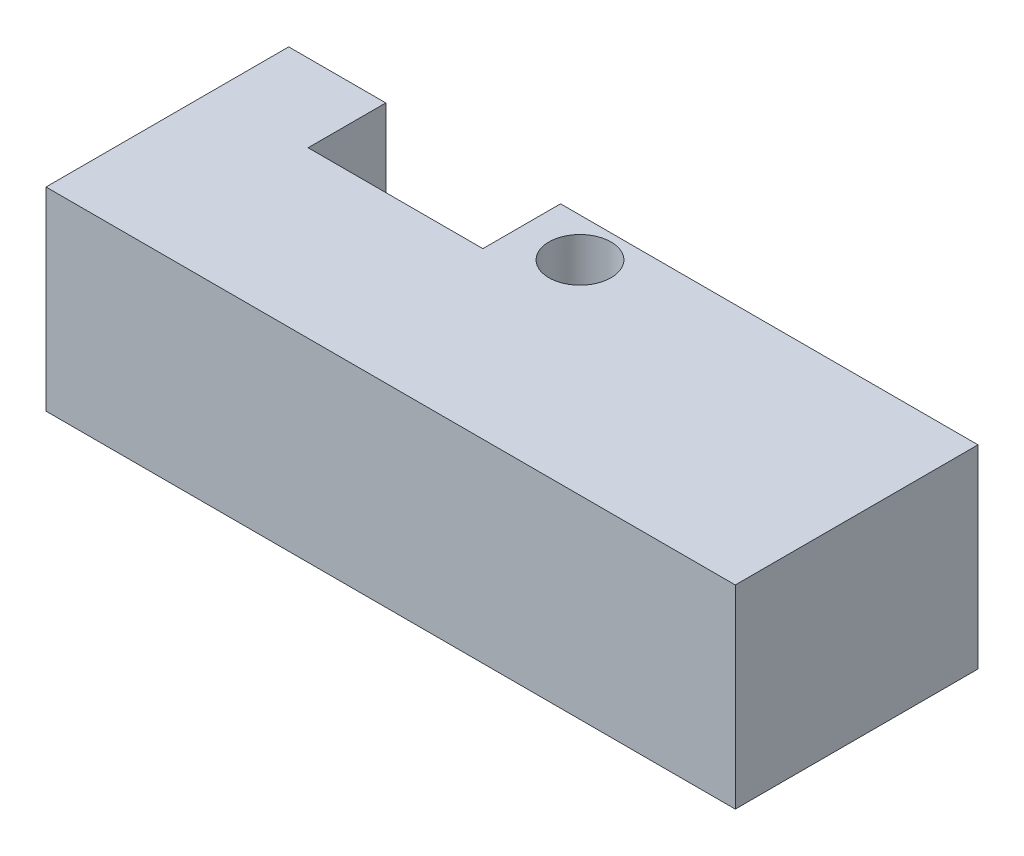
SolidWorks part; units mm, degrees
ref_plane "Front Plane" through (0, 0, 0) normal (0, 0, 1) x (1, 0, 0)
ref_plane "Top Plane" through (0, 0, 0) normal (0, 1, 0) x (1, 0, 0)
ref_plane "Right Plane" through (0, 0, 0) normal (1, 0, 0) x (0, 0, -1)
sketch "Sketch1" plane through (0, 0, 0) normal (0, 1, 0) x (1, 0, 0)
  line L1 (-17.75, -6.25) -> (17.75, -6.25)
  line L2 (-17.75, -6.25) -> (-17.75, 6.25)
  line L3 (-17.75, 6.25) -> (17.75, 6.25)
  line L4 (17.75, -6.25) -> (17.75, 6.25)
  line L5 (-17.75, -6.25) -> (17.75, 6.25) construction
  line L6 (-17.75, 6.25) -> (17.75, -6.25) construction
  point P0 (0, 0)
  dimension "D1" = 12.5
  dimension "D2" = 35.5
extrude "Boss-Extrude1" add sketch "Sketch1" along normal blind 10
sketch "Sketch2" plane through (0, 0, 0) normal (0, -1, 0) x (1, 0, 0)
  line L0 (-17.75, -6.25) -> (-17.75, 6.25) construction
  line L2 (-12.75, 1.25) -> (-12.75, -6.25)
  line L3 (17.75, -6.25) -> (-17.75, -6.25) construction
  line L4 (0, 6.25) -> (0, -6.25) construction
  line L5 (-17.75, 6.25) -> (17.75, 6.25) construction
  line L6 (12.75, 1.25) -> (12.75, -6.25)
  line L7 (-12.75, 1.25) -> (12.75, 1.25)
  line L8 (-12.75, -6.25) -> (12.75, -6.25)
  dimension "D1" = 7.5
  dimension "D2" = 5
extrude "Cut-Extrude1" cut sketch "Sketch2" against normal blind 7.5
sketch "Sketch4" plane through (0, 0, -6.25) normal (0, 0, -1) x (-1, 0, 0)
  line L0 (0, 0) -> (0, 10) construction
  line L1 (-17.75, 10) -> (17.75, 10) construction
  line L2 (-17.75, 10) -> (-17.75, 0) construction
  line L3 (-17.75, 0) -> (-12.75, 0) construction
  circle A0 centre (-14.75, 3) radius 1
  circle A1 centre (14.75, 3) radius 1
  dimension "D1" = 3
  dimension "D2" = 2
  dimension "D3" = 3
extrude "Cut-Extrude2" cut sketch "Sketch4" against normal blind 4
sketch "Sketch6" plane through (0, 0, -6.25) normal (0, 0, -1) x (-1, 0, 0)
  line L0 (-17.75, 10) -> (17.75, 10) construction
  line L1 (12.75, 7.5) -> (3.75, 7.5)
  line L2 (12.75, 7.5) -> (12.75, 10)
  line L3 (12.75, 10) -> (3.75, 10)
  line L4 (3.75, 7.5) -> (3.75, 10)
  dimension "D1" = 9
extrude "Cut-Extrude3" cut sketch "Sketch6" against normal blind 4
sketch "Sketch7" plane through (0, 10, 0) normal (0, 1, 0) x (1, 0, 0)
  line L0 (-3.75, 4.25) -> (17.75, 4.25) construction
  line L1 (-3.75, 2.25) -> (-3.75, 6.25) construction
  line L2 (17.75, -6.25) -> (17.75, 6.25) construction
  circle A0 centre (-0.75, 4.25) radius 1.6
  dimension "D1" = 3.2
  dimension "D2" = 3
extrude "Cut-Extrude4" cut sketch "Sketch7" against normal up to next and the other way through all
